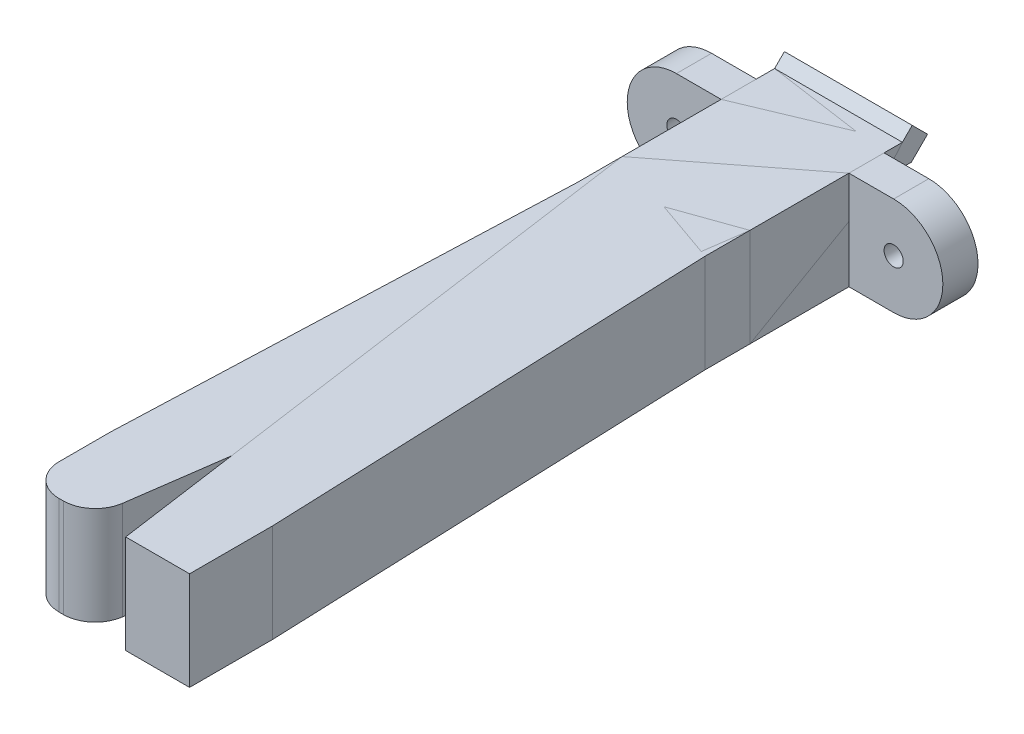
SolidWorks part; units mm, degrees
ref_plane "Front Plane" through (0, 0, 0) normal (0, 0, 1) x (1, 0, 0)
ref_plane "Top Plane" through (0, 0, 0) normal (0, 1, 0) x (1, 0, 0)
ref_plane "Right Plane" through (0, 0, 0) normal (1, 0, 0) x (0, 0, -1)
sketch "Sketch2" plane through (0, 0, 0) normal (0, 0, 1) x (1, 0, 0)
  line L0 (0, 5.9203) -> (0, 8.9503) construction
  line L1 (-5, -5.8182) -> (5, -5.8182)
  line L2 (-5, -5.8182) -> (-5, 8.9503)
  line L3 (-5, 8.9503) -> (5, 8.9503)
  line L4 (5, -5.8182) -> (5, 8.9503)
  line L7 (13.4766, 5.9203) -> (-18.5234, 5.9203) construction
  line L8 (0, -5.8182) -> (0, -2.7882) construction
  point P0 (0, 0)
  dimension "D1" = 10
extrude "Boss-Extrude1" add sketch "Sketch2" along normal blind 5
sketch "Sketch8" plane through (-5, 0, 0) normal (-1, 0, 0) x (0, 0, 1)
  line L6 (-0.15, 5.7703) -> (0, 5.7703)
  line L7 (0, 8.9503) -> (0, -5.8182) construction
  line L8 (0, 5.7703) -> (0, 4.0703)
  line L9 (0, 4.0703) -> (-0.15, 4.0703)
  line L11 (-0.15, -1.9297) -> (0, -1.9297)
  line L12 (-2.1379, 4.0703) -> (-0.15, 4.0703)
  line L13 (-0.15, 4.0703) -> (-0.15, 5.7703)
  line L14 (-0.15, 5.7703) -> (-1.4337, 5.7703)
  line L15 (-1.4337, 5.7703) -> (-2.2, 6.5366)
  line L16 (-2.2, 6.5366) -> (-3.4021, 5.3345)
  line L17 (-3.4021, 5.3345) -> (-2.1379, 4.0703)
  line L18 (-2.1379, 4.0703) -> (-0.15, 4.0703)
  line L20 (-0.15, 5.7703) -> (-1.4337, 5.7703)
  line L21 (-1.4337, 5.7703) -> (-2.2, 6.5366)
  line L22 (-2.2, 6.5366) -> (-3.4021, 5.3345)
  line L23 (-3.4021, 5.3345) -> (-2.1379, 4.0703)
  line L24 (-2.1379, -1.9297) -> (-0.15, -1.9297)
  line L25 (-0.15, -1.9297) -> (-0.15, -0.2297)
  line L26 (-0.15, -0.2297) -> (-1.4337, -0.2297)
  line L27 (-1.4337, -0.2297) -> (-2.2, 0.5366)
  line L28 (-2.2, 0.5366) -> (-3.4021, -0.6655)
  line L29 (-3.4021, -0.6655) -> (-2.1379, -1.9297)
  line L30 (-2.1379, -1.9297) -> (-0.15, -1.9297)
  line L32 (-0.15, -0.2297) -> (-1.4337, -0.2297)
  line L33 (-1.4337, -0.2297) -> (-2.2, 0.5366)
  line L34 (-2.2, 0.5366) -> (-3.4021, -0.6655)
  line L35 (-3.4021, -0.6655) -> (-2.1379, -1.9297)
  line L37 (-0.15, -0.2297) -> (0, -0.2297)
  line L38 (0, -1.9297) -> (0, -0.2297)
  dimension "D1" = 0.15
  dimension "D2" = 0.15
extrude "Boss-Extrude4" add sketch "Sketch8" against normal up to surface (10 mm away) up to face at (5, 1.566, 2.5)
sketch "Sketch9" plane through (0, 0, 0) normal (0, 0, -1) x (-1, 0, 0)
  line L4 (-5, 8.9503) -> (-5, 5.7703)
  line L5 (-5, 5.7703) -> (5, 5.7703)
  line L6 (5, 5.7703) -> (5, 8.9503)
  line L7 (5, 8.9503) -> (-5, 8.9503)
  line L8 (-5, 8.9503) -> (-5, 5.7703)
  line L10 (5, 5.7703) -> (5, 8.9503)
  line L11 (5, 8.9503) -> (-5, 8.9503)
  line L16 (5, -1.9297) -> (-5, -1.9297)
  line L17 (-5, -1.9297) -> (-5, -5.8182)
  line L18 (-5, -5.8182) -> (5, -5.8182)
  line L19 (5, -5.8182) -> (5, -1.9297)
  line L21 (-5, -1.9297) -> (-5, -5.8182)
  line L22 (-5, -5.8182) -> (5, -5.8182)
  line L23 (5, -5.8182) -> (5, -1.9297)
  line L26 (-5, 5.7703) -> (5, 5.7703)
  line L27 (5, -1.9297) -> (-5, -1.9297)
  dimension "D1" = 0
  dimension "D2" = 0
extrude "Cut-Extrude3" cut sketch "Sketch9" against normal blind 5
sketch "Sketch10" plane through (0, 5.7703, 0) normal (0, 1, 0) x (1, 0, 0)
  line L0 (-5, -5) -> (-5, -10.5)
  line L1 (-5, -10.5) -> (1.3524, -55.7)
  line L2 (1.3524, -55.7) -> (6.3524, -55.7)
  line L3 (-5, -5) -> (5, -5)
  line L4 (-120.9789, 453.7107) -> (412.3545, 453.7107) construction
  line L5 (6.3524, -55.7) -> (6.3524, -49.2)
  line L6 (5, -5) -> (5, -14)
  line L7 (5, -14) -> (6.3524, -49.2)
  dimension "D1" = 172
  dimension "D2" = 45.2
  dimension "D3" = 5
  dimension "D4" = 6.5
  dimension "D5" = 5.5
  dimension "D6" = 9
extrude "Boss-Extrude5" add sketch "Sketch10" against normal up to surface (7.7 mm away) up to face at (0, -1.9297, 1.4311)
ref_plane "Plane1" through (0, 0, 2.75) normal (0, 0, 1) x (1, 0, 0)
sketch "Sketch12" plane through (0, 0, 0) normal (0, 0, 1) x (1, 0, 0)
  line L0 (5, 5.7703) -> (8.5, 5.7703)
  line L1 (8.5, -1.9297) -> (5, -1.9297)
  line L2 (5, -1.9297) -> (5, 5.7703)
  line L3 (1.3524, 5.7703) -> (6.3524, 5.7703) construction
  line L4 (1.3524, -1.9297) -> (6.3524, -1.9297) construction
  line L5 (5, 5.3345) -> (5, 6.5366) construction
  line L6 (6.3524, 5.7703) -> (5, 5.7703) construction
  arc A0 (8.5, 5.7703) -> (8.5, -1.9297) centre (8.5, 1.9203) cw
  circle A1 centre (8.5, 1.9203) radius 0.75
  dimension "D1" = 1.5
  dimension "D2" = 3.5
extrude "Boss-Extrude7" add sketch "Sketch12" along normal up to surface (2.75 mm away) up to plane "Plane1"
mirror "Mirror1" about plane through (0, 0, 0) normal (1, 0, 0) of bodies 112
fillet "Fillet1" radius 2.5 4 edges at (-6.3524, 1.9203, 49.2) (-5, 1.9203, 14) (-1.3524, 1.9203, 55.7) (-6.3524, 1.9203, 55.7)
